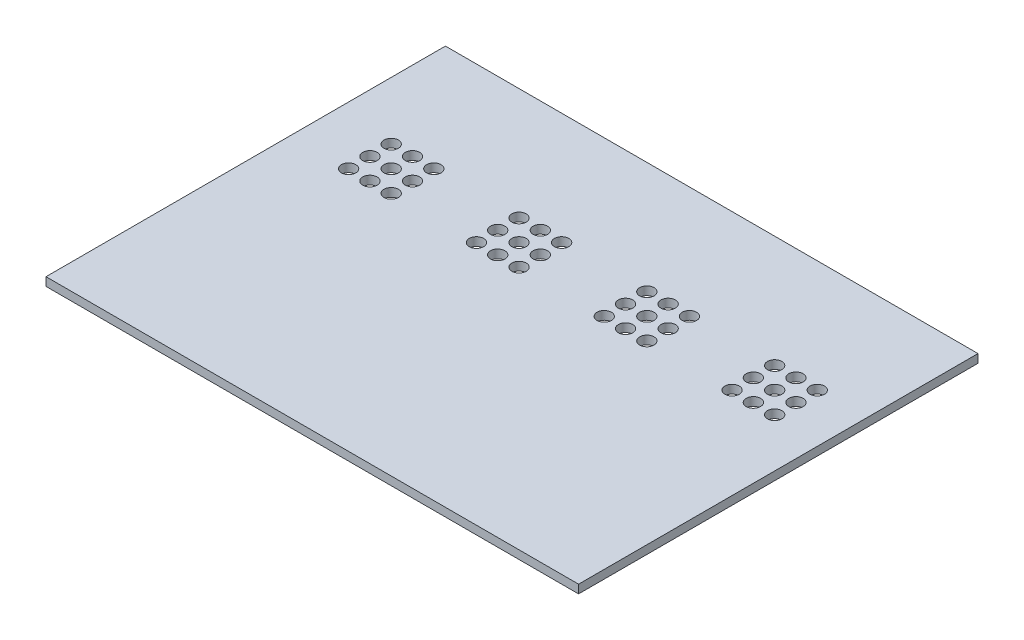
SolidWorks part; units mm, degrees
ref_plane "Front Plane" through (0, 0, 0) normal (0, 0, 1) x (1, 0, 0)
ref_plane "Top Plane" through (0, 0, 0) normal (0, 1, 0) x (1, 0, 0)
ref_plane "Right Plane" through (0, 0, 0) normal (1, 0, 0) x (0, 0, -1)
sketch "Sketch1" plane through (0, 0, 0) normal (0, 1, 0) x (1, 0, 0)
  line L1 (0, 0) -> (100, 0)
  line L2 (0, 0) -> (0, 75)
  line L3 (0, 75) -> (100, 75)
  line L4 (100, 0) -> (100, 75)
extrude "Boss-Extrude1" add sketch "Sketch1" along normal blind 1.5875
sketch "Sketch2" plane through (0, 0, 0) normal (0, 1, 0) x (1, 0, 0)
  line L1 (3.72, 39.3) -> (24.25, 39.3)
  line L2 (3.72, 39.3) -> (3.72, 35.5)
  line L3 (3.72, 35.5) -> (24.25, 35.5)
  line L4 (24.25, 39.3) -> (24.25, 35.5)
extrude "Boss-Extrude2" [suppressed] add sketch "Sketch2" along normal blind 4.5875
pattern_linear "LPattern1" [suppressed] count 4 spacing 24 count 2 spacing 25
sketch "Sketch3" plane through (0, 0, -75) normal (0, 0, -1) x (-1, 0, 0)
  line L1 (-5.75, -1.375) -> (-22, -1.375)
  line L2 (-5.75, -1.375) -> (-5.75, 2.875)
  line L3 (-5.75, 2.875) -> (-22, 2.875)
  line L4 (-22, -1.375) -> (-22, 2.875)
sketch "Sketch4" plane through (0, 1.5875, 0) normal (0, 1, 0) x (1, 0, 0)
  line L0 (0, 53.96) -> (100, 53.96) construction
  line L1 (0, 75) -> (0, 0) construction
  line L2 (100, 0) -> (100, 75) construction
  line L4 (0, 49.96) -> (100, 49.96) construction
  line L6 (0, 45.96) -> (100, 45.96) construction
  circle A0 centre (10.86, 53.96) radius 1.35
  circle A1 centre (10.86, 49.96) radius 1.35
  circle A2 centre (10.86, 45.96) radius 1.35
  circle A3 centre (14.86, 53.96) radius 1.35
  circle A4 centre (14.86, 49.96) radius 1.35
  circle A5 centre (14.86, 45.96) radius 1.35
  circle A6 centre (18.86, 53.96) radius 1.35
  circle A7 centre (18.86, 49.96) radius 1.35
  circle A8 centre (18.86, 45.96) radius 1.35
  circle A9 centre (34.86, 53.96) radius 1.35
  circle A10 centre (34.86, 49.96) radius 1.35
  circle A11 centre (34.86, 45.96) radius 1.35
  circle A12 centre (38.86, 53.96) radius 1.35
  circle A13 centre (38.86, 49.96) radius 1.35
  circle A14 centre (38.86, 45.96) radius 1.35
  circle A15 centre (42.86, 53.96) radius 1.35
  circle A16 centre (42.86, 49.96) radius 1.35
  circle A17 centre (42.86, 45.96) radius 1.35
  circle A18 centre (58.86, 53.96) radius 1.35
  circle A19 centre (58.86, 49.96) radius 1.35
  circle A20 centre (58.86, 45.96) radius 1.35
  circle A21 centre (62.86, 53.96) radius 1.35
  circle A22 centre (62.86, 49.96) radius 1.35
  circle A23 centre (62.86, 45.96) radius 1.35
  circle A24 centre (66.86, 53.96) radius 1.35
  circle A25 centre (66.86, 49.96) radius 1.35
  circle A26 centre (66.86, 45.96) radius 1.35
  circle A27 centre (82.86, 53.96) radius 1.35
  circle A28 centre (82.86, 49.96) radius 1.35
  circle A29 centre (82.86, 45.96) radius 1.35
  circle A30 centre (86.86, 53.96) radius 1.35
  circle A31 centre (86.86, 49.96) radius 1.35
  circle A32 centre (86.86, 45.96) radius 1.35
  circle A33 centre (90.86, 53.96) radius 1.35
  circle A34 centre (90.86, 49.96) radius 1.35
  circle A35 centre (90.86, 45.96) radius 1.35
  dimension "D1" = 3
  dimension "D2" = 4
extrude "Cut-Extrude1" cut sketch "Sketch4" against normal through all
